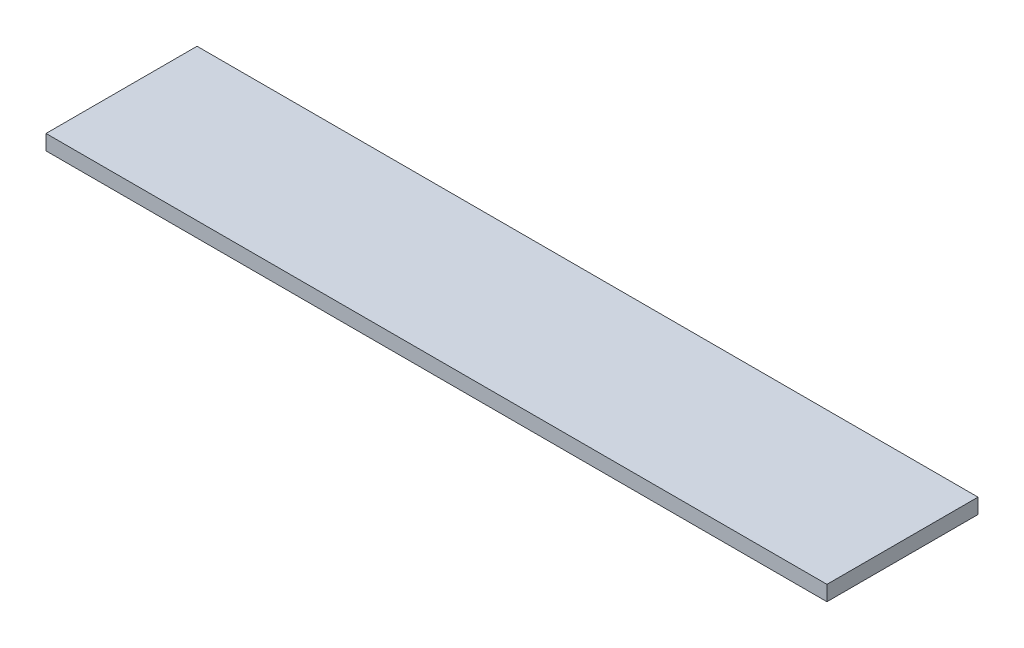
SolidWorks part; units mm, degrees
ref_plane "Face" through (0, 0, 0) normal (0, 0, 1) x (1, 0, 0)
ref_plane "Dessus" through (0, 0, 0) normal (0, 1, 0) x (1, 0, 0)
ref_plane "Droite" through (0, 0, 0) normal (1, 0, 0) x (0, 0, -1)
sketch "Esquisse1" plane through (0, 0, 0) normal (0, 1, 0) x (1, 0, 0)
  line L1 (0, 0) -> (517, 0)
  line L2 (0, 0) -> (0, 100)
  line L3 (0, 100) -> (517, 100)
  line L4 (517, 0) -> (517, 100)
  dimension "D1" = 517
  dimension "D2" = 100
extrude "Extrusion1" add sketch "Esquisse1" along normal blind 10
